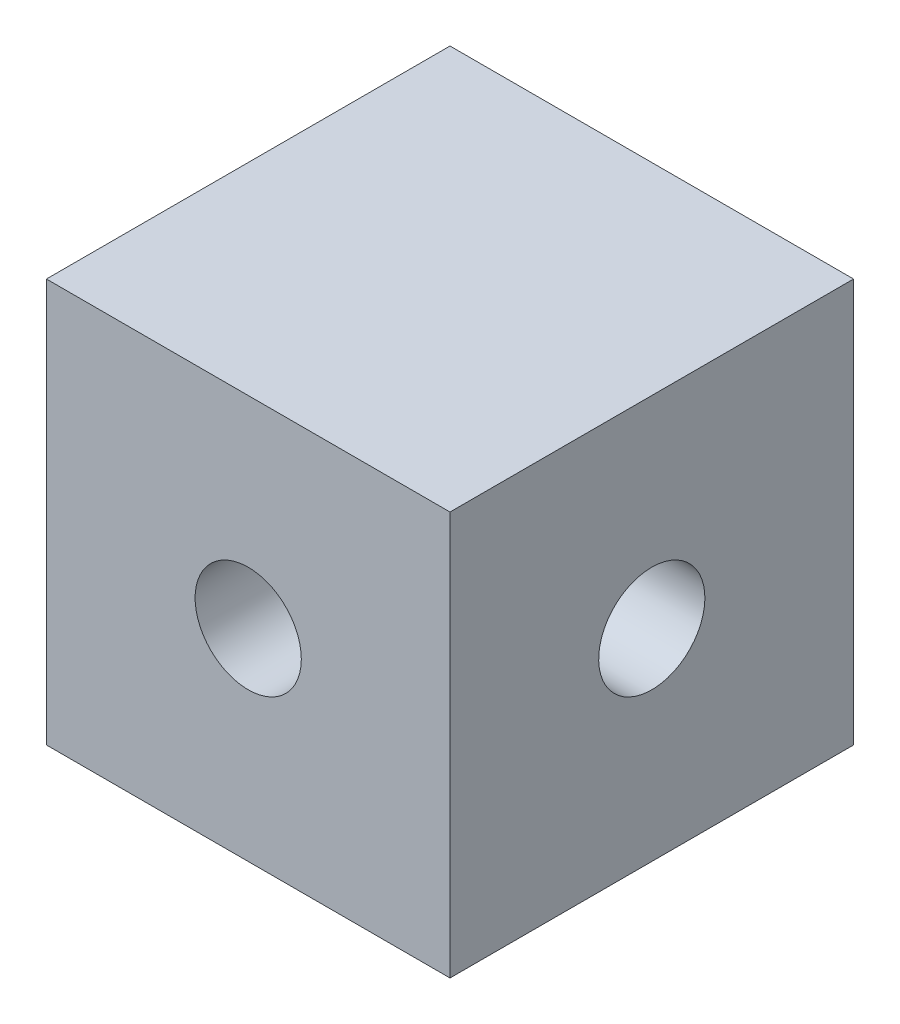
SolidWorks part; units mm, degrees
material "Cast Alloy Steel"
ref_plane "Front Plane" through (0, 0, 0) normal (0, 0, 1) x (1, 0, 0)
ref_plane "Top Plane" through (0, 0, 0) normal (0, 1, 0) x (1, 0, 0)
ref_plane "Right Plane" through (0, 0, 0) normal (1, 0, 0) x (0, 0, -1)
sketch "Sketch1" plane through (0, 0, 0) normal (0, 0, 1) x (1, 0, 0)
  line L1 (-9.5, 9.5) -> (9.5, 9.5)
  line L2 (-9.5, 9.5) -> (-9.5, -9.5)
  line L3 (-9.5, -9.5) -> (9.5, -9.5)
  line L4 (9.5, 9.5) -> (9.5, -9.5)
  line L5 (-9.5, 9.5) -> (9.5, -9.5) construction
  line L6 (-9.5, -9.5) -> (9.5, 9.5) construction
  point P0 (0, 0)
  dimension "D1" = 19
  dimension "D2" = 19
extrude "Boss-Extrude1" add sketch "Sketch1" along normal mid plane 19
sketch "Sketch2" plane through (0, 0, 9.5) normal (0, 0, 1) x (1, 0, 0)
  circle A0 centre (0, 0) radius 2.5
  dimension "D1" = 5
extrude "Cut-Extrude1" cut sketch "Sketch2" against normal blind 25
sketch "Sketch3" plane through (9.5, 0, 0) normal (1, 0, 0) x (0, 0, -1)
  circle A0 centre (0, 0) radius 2.5
  dimension "D1" = 5
extrude "Cut-Extrude2" cut sketch "Sketch3" against normal blind 25
